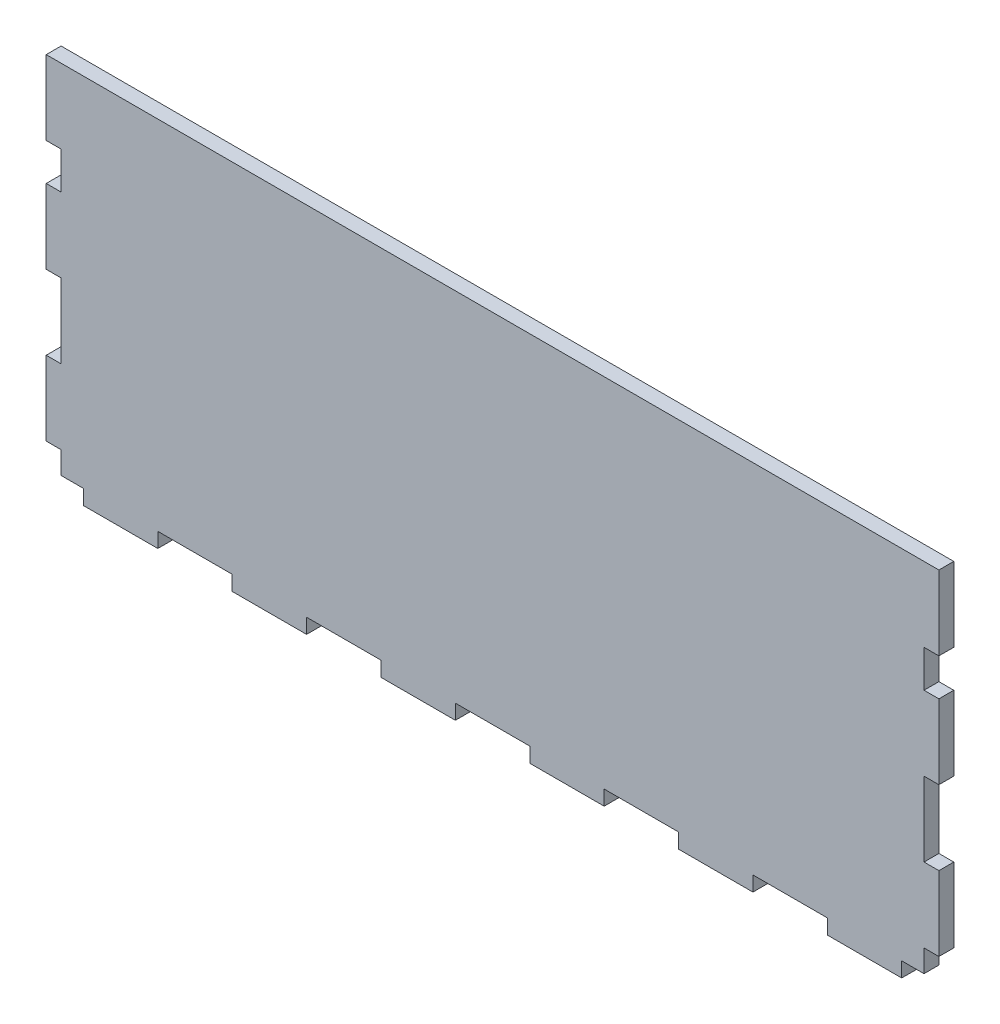
SolidWorks part; units mm, degrees
ref_plane "Front Plane" through (0, 0, 0) normal (0, 0, 1) x (1, 0, 0)
ref_plane "Top Plane" through (0, 0, 0) normal (0, 1, 0) x (1, 0, 0)
ref_plane "Right Plane" through (0, 0, 0) normal (1, 0, 0) x (0, 0, -1)
sketch "Sketch1" plane through (0, 0, 0) normal (0, 0, 1) x (1, 0, 0)
  line L0 (0, 0) -> (0, -127) construction
  line L1 (152.4, 0) -> (-152.4, 0)
  line L2 (12.7, -127) -> (-12.7, -127)
  line L3 (-12.7, -127) -> (-12.7, -121.92)
  line L4 (-12.7, -121.92) -> (-38.1, -121.92)
  line L5 (-38.1, -121.92) -> (-38.1, -127)
  line L6 (-38.1, -127) -> (-63.5, -127)
  line L7 (-63.5, -127) -> (-63.5, -121.92)
  line L8 (-63.5, -121.92) -> (-88.9, -121.92)
  line L9 (-88.9, -121.92) -> (-88.9, -127)
  line L10 (-88.9, -127) -> (-114.3, -127)
  line L11 (-152.4, -127) -> (-152.4, -114.3)
  line L12 (-114.3, -127) -> (-114.3, -121.92)
  line L13 (-114.3, -121.92) -> (-139.7, -121.92)
  line L14 (-139.7, -121.92) -> (-139.7, -127)
  line L15 (-139.7, -127) -> (-152.4, -127)
  line L16 (-152.4, -114.3) -> (-147.32, -114.3)
  line L17 (-147.32, -114.3) -> (-147.32, -88.9)
  line L18 (-147.32, -88.9) -> (-152.4, -88.9)
  line L19 (-152.4, -63.5) -> (-147.32, -63.5)
  line L20 (-147.32, -63.5) -> (-147.32, -38.1)
  line L21 (-147.32, -38.1) -> (-152.4, -38.1)
  line L22 (-152.4, -25.4) -> (-147.32, -25.4)
  line L23 (-147.32, -25.4) -> (-147.32, 0)
  line L24 (-152.4, -88.9) -> (-152.4, -63.5)
  line L25 (-152.4, -38.1) -> (-152.4, -25.4)
  line L26 (152.4, -38.1) -> (152.4, -25.4)
  line L27 (152.4, -88.9) -> (152.4, -63.5)
  line L28 (147.32, -25.4) -> (147.32, 0)
  line L29 (152.4, -25.4) -> (147.32, -25.4)
  line L30 (147.32, -38.1) -> (152.4, -38.1)
  line L31 (147.32, -63.5) -> (147.32, -38.1)
  line L32 (152.4, -63.5) -> (147.32, -63.5)
  line L33 (147.32, -88.9) -> (152.4, -88.9)
  line L34 (147.32, -114.3) -> (147.32, -88.9)
  line L35 (152.4, -114.3) -> (147.32, -114.3)
  line L36 (139.7, -127) -> (152.4, -127)
  line L37 (139.7, -121.92) -> (139.7, -127)
  line L38 (114.3, -121.92) -> (139.7, -121.92)
  line L39 (114.3, -127) -> (114.3, -121.92)
  line L40 (152.4, -127) -> (152.4, -114.3)
  line L41 (88.9, -127) -> (114.3, -127)
  line L42 (88.9, -121.92) -> (88.9, -127)
  line L43 (63.5, -121.92) -> (88.9, -121.92)
  line L44 (63.5, -127) -> (63.5, -121.92)
  line L45 (38.1, -127) -> (63.5, -127)
  line L46 (38.1, -121.92) -> (38.1, -127)
  line L47 (12.7, -121.92) -> (38.1, -121.92)
  line L48 (12.7, -127) -> (12.7, -121.92)
  line L49 (-147.32, 0) -> (147.32, 0)
  line L50 (-152.4, 0) -> (-152.4, -127)
  line L51 (-152.4, -127) -> (152.4, -127)
  line L52 (152.4, -127) -> (152.4, 0)
  line L53 (-147.32, 0) -> (-147.32, -114.3)
  line L54 (-139.7, -121.92) -> (139.7, -121.92)
  line L55 (147.32, 0) -> (147.32, -114.3)
  line L56 (-139.7, -121.92) -> (-152.4, -121.92)
  line L57 (139.7, -121.92) -> (152.4, -121.92)
  line L58 (-147.32, -114.3) -> (-147.32, -121.92)
  line L59 (147.32, -114.3) -> (147.32, -121.92)
  dimension "D1" = 152.4
  dimension "D2" = 127
  dimension "D3" = 12.7
  dimension "D4" = 25.4
  dimension "D5" = 5.08
  dimension "D6" = 12.7
  dimension "D7" = 25.4
extrude "Boss-Extrude1" add sketch "Sketch1" along normal mid plane 5.08 contours L1 L50 L22 L23 | L21 L50 L19 L20 | L18 L50 L16 L17 | L14 L51 L12 L13 | L9 L51 L7 L8 | L0 L49 L23 L53 L20 L17 L16 L11 L15 L14 L13 L54 L8 L4 | L1 L0 L54 L47 L43 L38 L37 L36 L40 L35 L34 L55 L31 L28 | L5 L51 L3 L4 | L44 L51 L42 L43 | L48 L51 L46 L47 | L39 L51 L37 L38 | L35 L52 L33 L34 | L32 L52 L30 L31 | L29 L52 L1 L28
